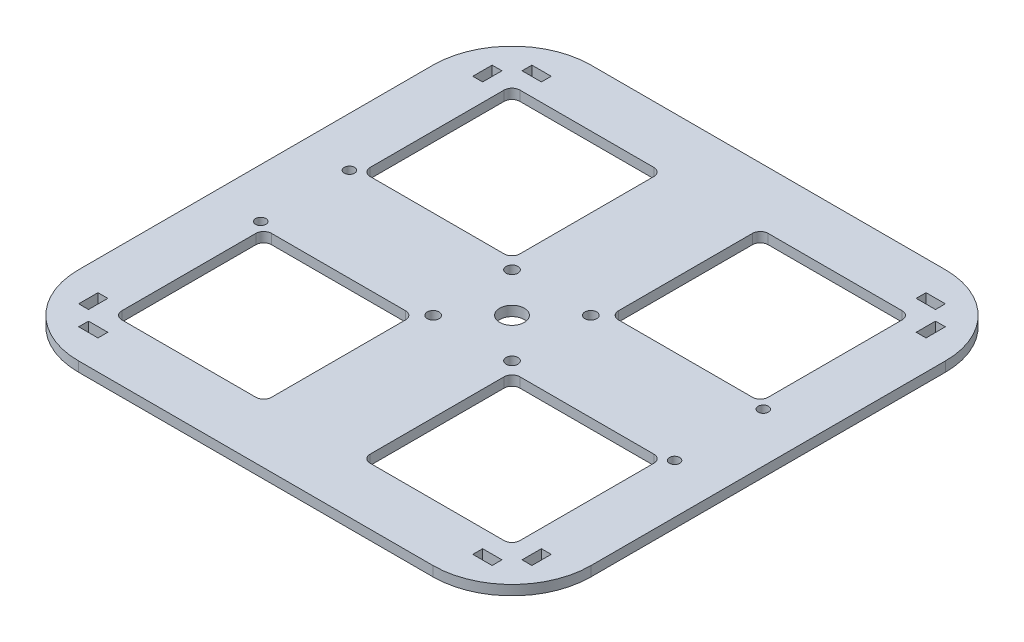
SolidWorks part; units mm, degrees
ref_plane "Front Plane" through (0, 0, 0) normal (0, 0, 1) x (1, 0, 0)
ref_plane "Top Plane" through (0, 0, 0) normal (0, 1, 0) x (1, 0, 0)
ref_plane "Right Plane" through (0, 0, 0) normal (1, 0, 0) x (0, 0, -1)
sketch "Sketch2" plane through (0, 0, 0) normal (0, 1, 0) x (1, 0, 0)
  line L0 (-146.05, -146.05) -> (146.05, -146.05) construction
  line L1 (-123.19, 128.27) -> (-36.83, 128.27)
  line L2 (-128.27, 123.19) -> (-128.27, 36.83)
  line L3 (-123.19, 31.75) -> (-36.83, 31.75)
  line L4 (-31.75, 123.19) -> (-31.75, 36.83)
  line L5 (36.83, 128.27) -> (123.19, 128.27)
  line L6 (31.75, 123.19) -> (31.75, 36.83)
  line L7 (36.83, 31.75) -> (123.19, 31.75)
  line L8 (128.27, 123.19) -> (128.27, 36.83)
  line L9 (-123.19, -31.75) -> (-36.83, -31.75)
  line L10 (-128.27, -36.83) -> (-128.27, -123.19)
  line L11 (-123.19, -128.27) -> (-36.83, -128.27)
  line L12 (-31.75, -36.83) -> (-31.75, -123.19)
  line L13 (36.83, -31.75) -> (123.19, -31.75)
  line L14 (31.75, -36.83) -> (31.75, -123.19)
  line L15 (36.83, -128.27) -> (123.19, -128.27)
  line L16 (128.27, -36.83) -> (128.27, -123.19)
  line L17 (-146.05, -146.05) -> (-146.05, 146.05) construction
  line L18 (-146.05, 146.05) -> (146.05, 146.05) construction
  line L19 (146.05, 146.05) -> (146.05, -146.05) construction
  line L20 (0, 206.5459) -> (0, -206.5459) construction
  line L21 (133.223, -146.05) -> (146.05, -146.05) construction
  line L22 (-133.223, -146.05) -> (-133.223, -139.7)
  line L23 (-133.223, -139.7) -> (-120.777, -139.7)
  line L24 (-120.777, -146.05) -> (-120.777, -139.7)
  line L25 (-206.5459, 0) -> (206.5459, 0) construction
  line L26 (-146.05, -146.05) -> (146.05, 146.05) construction
  line L27 (120.777, -146.05) -> (120.777, -139.7)
  line L28 (133.223, -139.7) -> (120.777, -139.7)
  line L29 (133.223, -146.05) -> (133.223, -139.7)
  line L30 (146.05, -146.05) -> (146.05, -133.223) construction
  line L31 (-146.05, 120.777) -> (-146.05, -120.777) construction
  line L32 (-146.05, 133.223) -> (-139.7, 133.223)
  line L33 (-139.7, 133.223) -> (-139.7, 120.777)
  line L34 (-146.05, 120.777) -> (-139.7, 120.777)
  line L35 (-146.05, -120.777) -> (-139.7, -120.777)
  line L36 (-139.7, -133.223) -> (-139.7, -120.777)
  line L37 (-146.05, -133.223) -> (-139.7, -133.223)
  line L38 (120.777, -146.05) -> (-120.777, -146.05) construction
  line L39 (133.223, 146.05) -> (146.05, 146.05) construction
  line L40 (133.223, 146.05) -> (133.223, 139.7)
  line L41 (133.223, 139.7) -> (120.777, 139.7)
  line L42 (120.777, 146.05) -> (120.777, 139.7)
  line L43 (-120.777, 146.05) -> (-120.777, 139.7)
  line L44 (-133.223, 139.7) -> (-120.777, 139.7)
  line L45 (-133.223, 146.05) -> (-133.223, 139.7)
  line L46 (146.05, 146.05) -> (146.05, 133.223) construction
  line L47 (-133.223, -146.05) -> (-146.05, -146.05) construction
  line L48 (146.05, -133.223) -> (139.7, -133.223)
  line L49 (139.7, -133.223) -> (139.7, -120.777)
  line L50 (146.05, -120.777) -> (139.7, -120.777)
  line L51 (146.05, 120.777) -> (139.7, 120.777)
  line L52 (139.7, 133.223) -> (139.7, 120.777)
  line L53 (146.05, 133.223) -> (139.7, 133.223)
  line L54 (146.05, 120.777) -> (146.05, -120.777) construction
  line L55 (-146.05, -146.05) -> (-146.05, -133.223) construction
  line L56 (-25.4, -25.4) -> (25.4, -25.4) construction
  line L57 (-25.4, -25.4) -> (-25.4, 25.4) construction
  line L58 (-25.4, 25.4) -> (25.4, 25.4) construction
  line L59 (25.4, -25.4) -> (25.4, 25.4) construction
  line L60 (-25.4, -25.4) -> (25.4, 25.4) construction
  line L61 (-25.4, 25.4) -> (25.4, -25.4) construction
  line L62 (-133.35, -28.575) -> (133.35, -28.575) construction
  line L63 (-133.35, -28.575) -> (-133.35, 28.575) construction
  line L64 (-133.35, 28.575) -> (133.35, 28.575) construction
  line L65 (133.35, -28.575) -> (133.35, 28.575) construction
  line L66 (-133.35, -28.575) -> (133.35, 28.575) construction
  line L67 (-133.35, 28.575) -> (133.35, -28.575) construction
  line L68 (-146.05, 133.223) -> (-146.05, 146.05) construction
  line L69 (-146.05, 146.05) -> (-133.223, 146.05) construction
  line L70 (120.777, 146.05) -> (-120.777, 146.05) construction
  line L71 (-133.223, -146.05) -> (-120.777, -146.05)
  line L72 (-114.3, -165.1) -> (114.3, -165.1)
  line L73 (-165.1, -114.3) -> (-165.1, 114.3)
  line L74 (-114.3, 165.1) -> (114.3, 165.1)
  line L75 (165.1, -114.3) -> (165.1, 114.3)
  line L76 (-165.1, -165.1) -> (165.1, 165.1) construction
  line L77 (-165.1, 165.1) -> (165.1, -165.1) construction
  line L78 (-146.05, -120.777) -> (-146.05, -133.223)
  line L79 (120.777, -146.05) -> (133.223, -146.05)
  line L80 (146.05, -120.777) -> (146.05, -133.223)
  line L81 (146.05, 133.223) -> (146.05, 120.777)
  line L82 (120.777, 146.05) -> (133.223, 146.05)
  line L83 (-133.223, 146.05) -> (-120.777, 146.05)
  line L84 (-146.05, 133.223) -> (-146.05, 120.777)
  circle A0 centre (0, 0) radius 206.5459 construction
  circle A1 centre (0, 0) radius 7.9375
  arc A2 (123.19, 128.27) -> (128.27, 123.19) centre (123.19, 123.19) cw
  arc A3 (36.83, 128.27) -> (31.75, 123.19) centre (36.83, 123.19) ccw
  arc A4 (31.75, 36.83) -> (36.83, 31.75) centre (36.83, 36.83) ccw
  arc A5 (123.19, 31.75) -> (128.27, 36.83) centre (123.19, 36.83) ccw
  arc A6 (123.19, -128.27) -> (128.27, -123.19) centre (123.19, -123.19) ccw
  arc A7 (123.19, -31.75) -> (128.27, -36.83) centre (123.19, -36.83) cw
  arc A8 (36.83, -31.75) -> (31.75, -36.83) centre (36.83, -36.83) ccw
  arc A9 (31.75, -123.19) -> (36.83, -128.27) centre (36.83, -123.19) ccw
  arc A10 (-128.27, -123.19) -> (-123.19, -128.27) centre (-123.19, -123.19) ccw
  arc A11 (-36.83, -128.27) -> (-31.75, -123.19) centre (-36.83, -123.19) ccw
  arc A12 (-36.83, -31.75) -> (-31.75, -36.83) centre (-36.83, -36.83) cw
  arc A13 (-123.19, -31.75) -> (-128.27, -36.83) centre (-123.19, -36.83) ccw
  arc A14 (-128.27, 36.83) -> (-123.19, 31.75) centre (-123.19, 36.83) ccw
  arc A15 (-36.83, 31.75) -> (-31.75, 36.83) centre (-36.83, 36.83) ccw
  arc A16 (-36.83, 128.27) -> (-31.75, 123.19) centre (-36.83, 123.19) cw
  arc A17 (-123.19, 128.27) -> (-128.27, 123.19) centre (-123.19, 123.19) ccw
  circle A18 centre (25.4, -25.4) radius 3.81
  circle A19 centre (25.4, 25.4) radius 3.81
  circle A20 centre (-25.4, 25.4) radius 3.81
  circle A21 centre (-25.4, -25.4) radius 3.81
  circle A22 centre (133.35, -28.575) radius 3.302
  circle A23 centre (-133.35, -28.575) radius 3.302
  circle A24 centre (-133.35, 28.575) radius 3.302
  circle A25 centre (133.35, 28.575) radius 3.302
  arc A26 (-114.3, -165.1) -> (-165.1, -114.3) centre (-114.3, -114.3) cw
  arc A27 (114.3, -165.1) -> (165.1, -114.3) centre (114.3, -114.3) ccw
  arc A28 (114.3, 165.1) -> (165.1, 114.3) centre (114.3, 114.3) cw
  arc A29 (-165.1, 114.3) -> (-114.3, 165.1) centre (-114.3, 114.3) cw
  point P22 (128.27, 128.27)
  point P25 (31.75, 128.27)
  point P28 (31.75, 31.75)
  point P35 (128.27, -31.75)
  point P38 (31.75, -31.75)
  point P41 (31.75, -128.27)
  point P46 (-31.75, -128.27)
  point P49 (-31.75, -31.75)
  point P52 (-128.27, -31.75)
  point P57 (-31.75, 31.75)
  point P60 (-31.75, 128.27)
  point P63 (-128.27, 128.27)
  dimension "D9" = 15.875
  dimension "D18" = 292.1
  dimension "D19" = 5.08
  dimension "D26" = 7.62
  dimension "D27" = 7.62
  dimension "D28" = 7.62
  dimension "D29" = 7.62
  dimension "D32" = 6.604
  dimension "D33" = 6.604
  dimension "D34" = 6.604
  dimension "D35" = 6.604
  dimension "D38" = 50.8
  dimension "D1" = 96.52
  dimension "D2" = 96.52
  dimension "D3" = 96.52
  dimension "D4" = 96.52
  dimension "D5" = 96.52
  dimension "D6" = 96.52
  dimension "D7" = 96.52
  dimension "D8" = 96.52
  dimension "D10" = 63.5
  dimension "D11" = 31.75
  dimension "D12" = 63.5
  dimension "D13" = 31.75
  dimension "D14" = 63.5
  dimension "D15" = 31.75
  dimension "D16" = 63.5
  dimension "D17" = 31.75
  dimension "D20" = 292.1
  dimension "D21" = 12.446
  dimension "D22" = 6.35
  dimension "D23" = 12.827
  dimension "D24" = 50.8
  dimension "D25" = 50.8
  dimension "D30" = 57.15
  dimension "D31" = 266.7
  dimension "D36" = 330.2
  dimension "D37" = 330.2
extrude "Boss-Extrude1" add sketch "Sketch2" along normal blind 6.35
